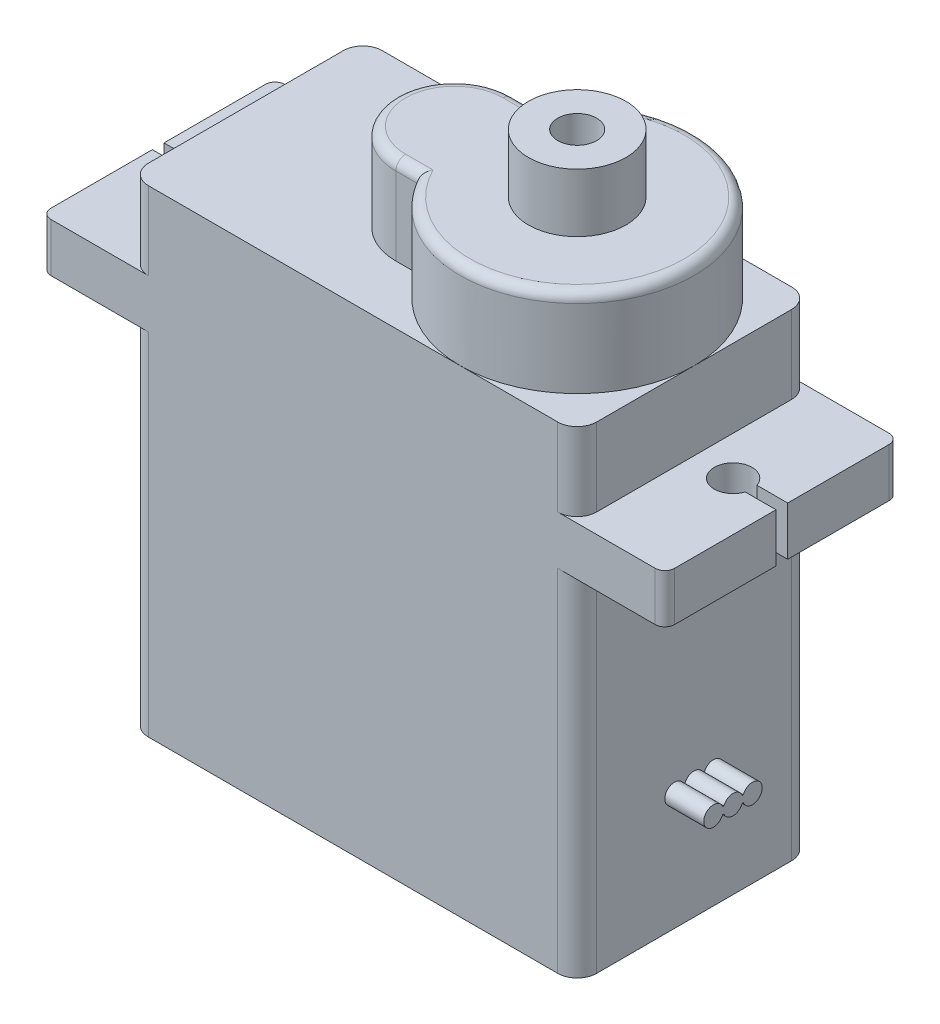
SolidWorks part; units mm, degrees
ref_plane "Front Plane" through (0, 0, 0) normal (0, 0, 1) x (1, 0, 0)
ref_plane "Top Plane" through (0, 0, 0) normal (0, 1, 0) x (1, 0, 0)
ref_plane "Right Plane" through (0, 0, 0) normal (1, 0, 0) x (0, 0, -1)
sketch "Sketch1" plane through (0, 0, 0) normal (0, 1, 0) x (1, 0, 0)
  line L1 (-11.5, 6) -> (11.5, 6)
  line L2 (-11.5, 6) -> (-11.5, -6)
  line L3 (-11.5, -6) -> (11.5, -6)
  line L4 (11.5, 6) -> (11.5, -6)
  line L5 (-11.5, 6) -> (11.5, -6) construction
  line L6 (-11.5, -6) -> (11.5, 6) construction
  point P0 (0, 0)
  dimension "D1" = 23
  dimension "D2" = 12
extrude "Boss-Extrude1" add sketch "Sketch1" along normal blind 18
sketch "Sketch2" plane through (0, 18, 0) normal (0, 1, 0) x (1, 0, 0)
  line L1 (-16, -6) -> (16, -6)
  line L2 (-16, -6) -> (-16, 6)
  line L3 (-16, 6) -> (16, 6)
  line L4 (16, -6) -> (16, 6)
  line L5 (-16, -6) -> (16, 6) construction
  line L6 (-16, 6) -> (16, -6) construction
  point P0 (0, 0)
  dimension "D1" = 32
  dimension "D2" = 12
extrude "Boss-Extrude2" add sketch "Sketch2" along normal blind 2.5
sketch "Sketch3" plane through (0, 20.5, 0) normal (0, 1, 0) x (1, 0, 0)
  line L0 (16, 6) -> (-16, 6) construction
  line L1 (-11.5, -6) -> (11.5, -6)
  line L2 (-11.5, -6) -> (-11.5, 6)
  line L3 (-11.5, 6) -> (11.5, 6)
  line L4 (11.5, -6) -> (11.5, 6)
  line L5 (-11.5, -6) -> (11.5, 6) construction
  line L6 (-11.5, 6) -> (11.5, -6) construction
  point P0 (0, 0)
  dimension "D1" = 23
extrude "Boss-Extrude3" add sketch "Sketch3" along normal blind 4
sketch "Sketch4" plane through (0, 24.5, 0) normal (0, 1, 0) x (1, 0, 0)
  line L0 (-11.5, -6) -> (11.5, -6) construction
  line L1 (11.5, 6) -> (-11.5, 6) construction
  line L2 (11.5, -6) -> (11.5, 6) construction
  line L3 (-0.8028, 3) -> (0.3038, 3)
  line L4 (-0.8028, 0) -> (0, 0) construction
  line L5 (-0.8028, -3) -> (0.3038, -3)
  arc A0 (0.3038, -3) -> (0.3038, 3) centre (5.5, 0) ccw
  arc A1 (-0.8028, 3) -> (-0.8028, -3) centre (-0.8028, 0) ccw
  dimension "D1" = 6
  dimension "D2" = 0.8028
extrude "Boss-Extrude4" add sketch "Sketch4" along normal blind 4.5
fillet "Fillet1" radius 1 8 edges at (11.5, 9, -6) (11.5, 22.5, -6) (-11.5, 22.5, -6) (-11.5, 9, -6) (11.5, 9, 6) (11.5, 22.5, 6) (-11.5, 22.5, 6) (-11.5, 9, 6)
fillet "Fillet2" radius 0.5 4 edges at (-16, 19.25, 6) (-16, 19.25, -6) (16, 19.25, -6) (16, 19.25, 6)
sketch "Sketch7" plane through (0, 20.5, 0) normal (0, 1, 0) x (1, 0, 0)
  line L0 (16, -5.5) -> (16, 5.5) construction
  line L1 (14.4206, 0.3) -> (16, 0.3)
  line L2 (16, 0.3) -> (16, -0.3)
  line L3 (16, -0.3) -> (14.4206, -0.3)
  arc A0 (14.4206, 0.3) -> (14.4206, -0.3) centre (13.5, 0) ccw
  dimension "D1" = 2.5
  dimension "D2" = 0.3
  dimension "D3" = 0.3
extrude "Cut-Extrude2" cut sketch "Sketch7" against normal through all
mirror "Mirror1" about plane through (0, 0, 0) normal (1, 0, 0) of "Cut-Extrude2"
sketch "Sketch5" plane through (0, 29, 0) normal (0, 1, 0) x (1, 0, 0)
  circle A0 centre (5.5, 0) radius 2.5
extrude "Boss-Extrude5" add sketch "Sketch5" along normal blind 3
sketch "Sketch6" plane through (0, 32, 0) normal (0, 1, 0) x (1, 0, 0)
  circle A0 centre (5.5, 0) radius 1
extrude "Cut-Extrude1" cut sketch "Sketch6" against normal blind 3
sketch "Sketch8" plane through (11.5, 0, 0) normal (1, 0, 0) x (0, 0, -1)
  line L2 (-0.5392, 6.1768) -> (-0.4746, 6.1768)
  line L4 (0.5254, 5.8232) -> (0.4608, 5.8232)
  line L5 (0.4608, 6.1768) -> (0.5254, 6.1768)
  line L6 (-0.4746, 5.8232) -> (-0.5392, 5.8232)
  arc A0 (-0.4746, 5.8232) -> (0.4608, 5.8232) centre (-0.0069, 6) ccw
  arc A1 (0.5254, 5.8232) -> (0.5254, 6.1768) centre (0.9931, 6) ccw
  arc A2 (-0.5392, 6.1768) -> (-0.5392, 5.8232) centre (-1.0069, 6) ccw
  arc A3 (0.4608, 6.1768) -> (-0.4746, 6.1768) centre (-0.0069, 6) ccw
  dimension "D1" = 6
extrude "Boss-Extrude11" add sketch "Sketch8" along normal blind 2 contours A1
fillet "Fillet3" radius 0.5 4 edges at (-0.2495, 29, 3) (-3.8028, 29, 0) (-0.2495, 29, -3) (11.5, 29, 0)
